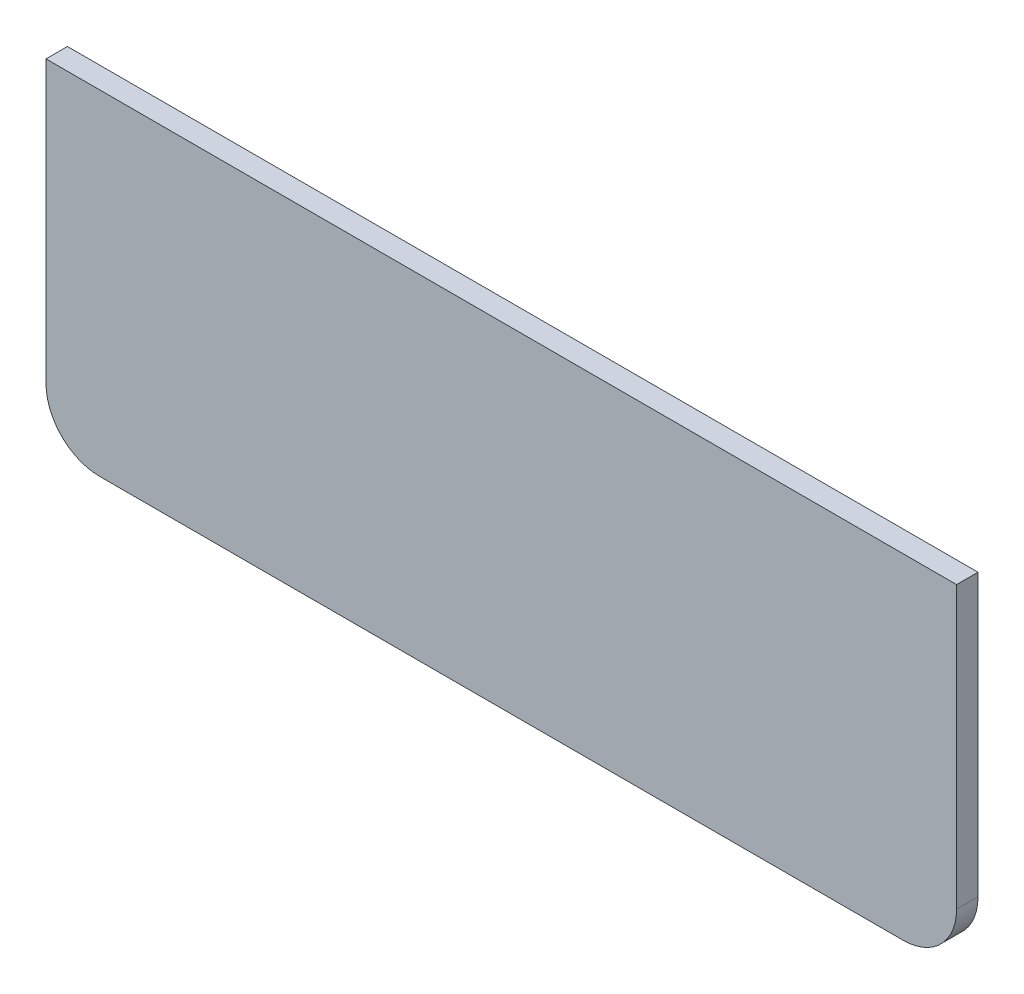
SolidWorks part; units mm, degrees
ref_plane "Спереди" through (0, 0, 0) normal (0, 0, 1) x (1, 0, 0)
ref_plane "Сверху" through (0, 0, 0) normal (0, 1, 0) x (1, 0, 0)
ref_plane "Справа" through (0, 0, 0) normal (1, 0, 0) x (0, 0, -1)
sketch "Эскиз1" plane through (0, 0, 0) normal (0, 0, 1) x (1, 0, 0)
  line L1 (-30, -12.5) -> (30, -12.5)
  line L2 (-34, -8.5) -> (-34, 12.5)
  line L3 (-34, 12.5) -> (34, 12.5)
  line L4 (34, -8.5) -> (34, 12.5)
  line L5 (-34, -12.5) -> (34, 12.5) construction
  line L6 (-34, 12.5) -> (34, -12.5) construction
  arc A0 (30, -12.5) -> (34, -8.5) centre (30, -8.5) ccw
  arc A1 (-30, -12.5) -> (-34, -8.5) centre (-30, -8.5) cw
  point P0 (0, 0)
  dimension "D3" = 4
  dimension "D1" = 68
  dimension "D2" = 25
extrude "Бобышка-Вытянуть1" add sketch "Эскиз1" along normal blind 1.6
